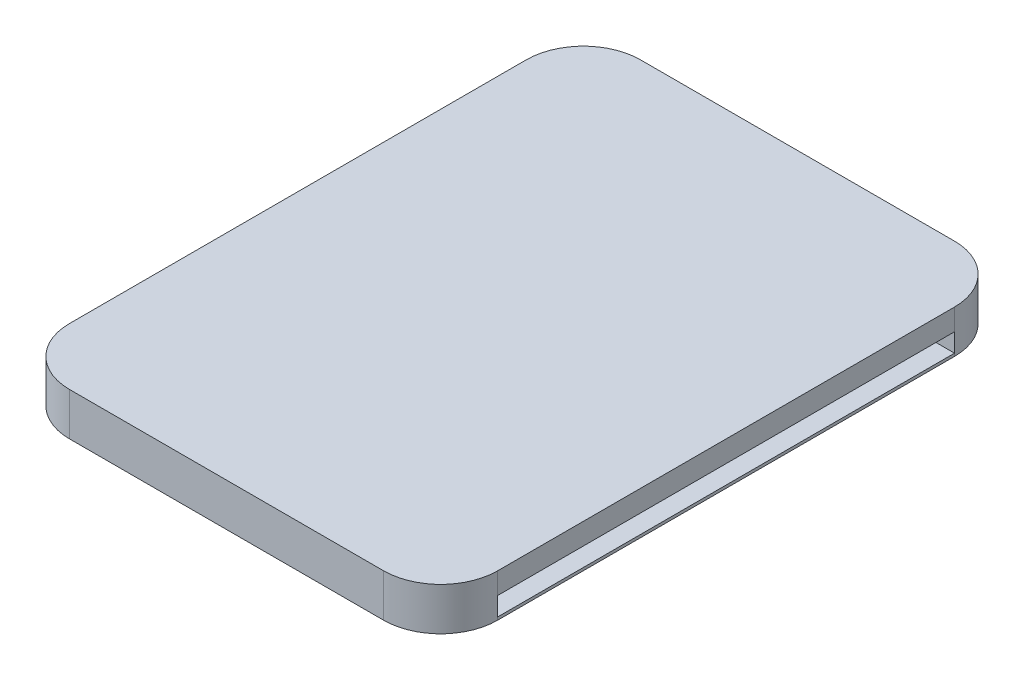
SolidWorks part; units mm, degrees
material "Alloy Steel"
ref_plane "Front Plane" through (0, 0, 0) normal (0, 0, 1) x (1, 0, 0)
ref_plane "Top Plane" through (0, 0, 0) normal (0, 1, 0) x (1, 0, 0)
ref_plane "Right Plane" through (0, 0, 0) normal (1, 0, 0) x (0, 0, -1)
sketch "Sketch1" plane through (0, 0, 0) normal (0, 1, 0) x (1, 0, 0)
  line L1 (-550, 1000) -> (-225, 1000)
  line L2 (-750, 800) -> (-750, -800)
  line L3 (-550, -1000) -> (550, -1000)
  line L4 (750, 800) -> (750, -800)
  line L5 (-750, 1000) -> (750, -1000) construction
  line L6 (-750, -1000) -> (750, 1000) construction
  line L9 (225, 1000) -> (550, 1000)
  line L10 (-225, 1000) -> (225, 1000)
  arc A0 (-750, -800) -> (-550, -1000) centre (-550, -800) ccw
  arc A1 (550, -1000) -> (750, -800) centre (550, -800) ccw
  arc A2 (-750, 800) -> (-550, 1000) centre (-550, 800) cw
  arc A3 (550, 1000) -> (750, 800) centre (550, 800) cw
  point P0 (0, 0)
  point P19 (0, 1000)
  dimension "D3" = 200
  dimension "D1" = 1500
  dimension "D2" = 2000
  dimension "D4" = 450
extrude "Boss-Extrude1" add sketch "Sketch1" along normal blind 150
sketch "Sketch2" plane through (750, 0, 0) normal (1, 0, 0) x (0, 0, -1)
  line L0 (-800, 0) -> (800, 0) construction
  line L1 (-200, 75) -> (200, 75)
  line L2 (-200, 75) -> (-200, 10)
  line L3 (-200, 10) -> (200, 10)
  line L4 (200, 75) -> (200, 10)
  line L5 (-200, 75) -> (200, 10) construction
  line L6 (-200, 10) -> (200, 75) construction
  point P0 (0, 42.5)
  dimension "D1" = 400
  dimension "D2" = 65
  dimension "D3" = 10
extrude "Cut-Extrude1" cut sketch "Sketch2" against normal through all both and the other way through all
sketch "Sketch3" plane through (750, 0, 0) normal (1, 0, 0) x (0, 0, -1)
  line L1 (200, 10) -> (800, 10)
  line L2 (200, 10) -> (200, 75)
  line L3 (200, 75) -> (800, 75)
  line L4 (800, 10) -> (800, 75)
  line L5 (-200, 10) -> (-800, 10)
  line L6 (-200, 10) -> (-200, 75)
  line L7 (-200, 75) -> (-800, 75)
  line L8 (-800, 10) -> (-800, 75)
  dimension "D1" = 600
extrude "Cut-Extrude2" cut sketch "Sketch3" against normal blind 130
mirror "Mirror1" about plane through (0, 0, 0) normal (1, 0, 0) of "Cut-Extrude2"
sketch "Sketch4" plane through (0, 150, 0) normal (0, 1, 0) x (1, 0, 0)
  line L0 (-670, 100) -> (-670, -100) construction
  line L1 (-750, 800) -> (-750, -800) construction
  line L2 (750, 0) -> (-750, 0) construction
  line L3 (750, -800) -> (750, 800) construction
  circle A0 centre (-670, 100) radius 5
  circle A1 centre (-670, -100) radius 5
  point P8 (-670, 0)
  dimension "D3" = 10
  dimension "D1" = 200
  dimension "D2" = 80
extrude "Boss-Extrude2" add sketch "Sketch4" against normal blind 150
mirror "Mirror2" about plane through (0, 0, 0) normal (1, 0, 0) of "Boss-Extrude2"
sketch "Sketch5" plane through (0, 150, 0) normal (0, 1, 0) x (1, 0, 0)
  line L0 (-350, -480) -> (-350, -600) construction
  line L1 (-315, -480) -> (-315, -600)
  line L2 (-385, -480) -> (-385, -600)
  line L3 (350, -480) -> (350, -600) construction
  line L4 (385, -480) -> (385, -600)
  line L5 (315, -480) -> (315, -600)
  line L6 (-750, 800) -> (-750, -800) construction
  line L7 (750, -800) -> (750, 800) construction
  line L8 (-550, -1000) -> (550, -1000) construction
  arc A0 (-315, -480) -> (-385, -480) centre (-350, -480) ccw
  arc A1 (-385, -600) -> (-315, -600) centre (-350, -600) ccw
  arc A2 (385, -480) -> (315, -480) centre (350, -480) ccw
  arc A3 (315, -600) -> (385, -600) centre (350, -600) ccw
  point P2 (-350, -540)
  point P7 (350, -540)
  dimension "D1" = 35
  dimension "D2" = 120
  dimension "D3" = 400
  dimension "D4" = 400
  dimension "D5" = 400
  dimension "D6" = 400
sketch "Sketch6" plane through (0, 0, -1000) normal (0, 0, -1) x (-1, 0, 0)
  line L1 (-377.5, 105) -> (-322.5, 105)
  line L2 (-377.5, 105) -> (-377.5, 45)
  line L3 (-377.5, 45) -> (-322.5, 45)
  line L4 (-322.5, 105) -> (-322.5, 45)
  line L5 (-377.5, 105) -> (-322.5, 45) construction
  line L6 (-377.5, 45) -> (-322.5, 105) construction
  line L7 (322.5, 105) -> (377.5, 105)
  line L8 (322.5, 105) -> (322.5, 45)
  line L9 (322.5, 45) -> (377.5, 45)
  line L10 (377.5, 105) -> (377.5, 45)
  line L11 (322.5, 105) -> (377.5, 45) construction
  line L12 (322.5, 45) -> (377.5, 105) construction
  line L13 (-550, 150) -> (550, 150) construction
  line L15 (-550, 150) -> (-550, 0) construction
  line L16 (550, 150) -> (550, 0) construction
  point P0 (-350, 75)
  point P5 (350, 75)
  dimension "D1" = 55
  dimension "D2" = 60
  dimension "D3" = 200
  dimension "D4" = 45
  dimension "D5" = 200
extrude "Cut-Extrude4" cut sketch "Sketch6" against normal blind 200
sketch "Sketch7" plane through (0, 0, 0) normal (0, -1, 0) x (1, 0, 0)
  line L2 (385, 480) -> (385, 600)
  line L3 (315, 600) -> (315, 480)
  line L4 (385, 480) -> (385, 600)
  line L5 (315, 600) -> (315, 480)
  line L6 (-315, 480) -> (-315, 600)
  line L7 (-385, 600) -> (-385, 480)
  line L8 (-315, 480) -> (-315, 600)
  line L9 (-385, 600) -> (-385, 480)
  arc A2 (385, 600) -> (315, 600) centre (350, 600) ccw
  arc A3 (315, 480) -> (385, 480) centre (350, 480) ccw
  arc A4 (385, 600) -> (315, 600) centre (350, 600) ccw
  arc A5 (315, 480) -> (385, 480) centre (350, 480) ccw
  arc A6 (-315, 600) -> (-385, 600) centre (-350, 600) ccw
  arc A7 (-385, 480) -> (-315, 480) centre (-350, 480) ccw
  arc A8 (-315, 600) -> (-385, 600) centre (-350, 600) ccw
  arc A9 (-385, 480) -> (-315, 480) centre (-350, 480) ccw
  dimension "D1" = 0
  dimension "D2" = 0
extrude "Cut-Extrude5" cut sketch "Sketch7" against normal blind 130
ref_plane "Plane1" through (0, 0, 200) normal (0, 0, -1) x (-1, 0, 0)
sketch "Sketch8" plane through (0, 0, 200) normal (0, 0, -1) x (-1, 0, 0)
  line L1 (-615, 70) -> (615, 70)
  line L2 (-615, 70) -> (-615, 15)
  line L3 (-615, 15) -> (615, 15)
  line L4 (620, 10) -> (620, 75)
  line L5 (620, 75) -> (-620, 75)
  line L6 (-620, 75) -> (-620, 10)
  line L7 (-620, 10) -> (620, 10)
  line L8 (620, 10) -> (620, 75) construction
  line L9 (620, 75) -> (-620, 75) construction
  line L10 (-620, 75) -> (-620, 10) construction
  line L11 (-620, 10) -> (620, 10) construction
  line L12 (615, 70) -> (615, 15)
  line L13 (-615, 70) -> (615, 15) construction
  line L14 (-615, 15) -> (615, 70) construction
  point P2 (0, 42.5)
  point P9 (620, 42.5)
  dimension "D2" = 5
  dimension "D3" = 5
  dimension "D4" = 5
  dimension "D5" = 5
  dimension "D1" = 0
extrude "Cut-Extrude6" cut sketch "Sketch8" against normal blind 600
sketch "Sketch9" plane through (0, 0, -1000) normal (0, 0, -1) x (-1, 0, 0)
  line L0 (0, 200.1102) -> (0, -70.8291) construction
  line L1 (-440, 142.5) -> (-260, 142.5)
  line L2 (-440, 142.5) -> (-440, 7.5)
  line L3 (-440, 7.5) -> (-260, 7.5)
  line L4 (-260, 142.5) -> (-260, 7.5)
  line L5 (-440, 142.5) -> (-260, 7.5) construction
  line L6 (-440, 7.5) -> (-260, 142.5) construction
  line L7 (440, 7.5) -> (260, 7.5)
  line L8 (260, 142.5) -> (260, 7.5)
  line L9 (440, 142.5) -> (260, 142.5)
  line L10 (440, 142.5) -> (440, 7.5)
  point P0 (-350, 75)
  dimension "D1" = 180
  dimension "D2" = 135
extrude "Cut-Extrude7" cut sketch "Sketch9" against normal blind 120
